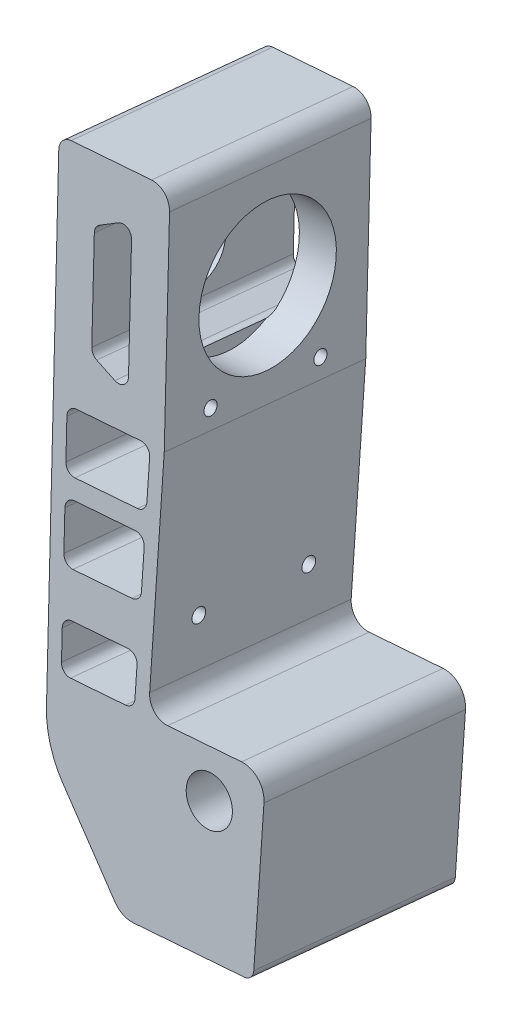
SolidWorks part; units mm, degrees
ref_plane "Front Plane" through (0, 0, 0) normal (0, 0, 1) x (1, 0, 0)
ref_plane "Top Plane" through (0, 0, 0) normal (0, 1, 0) x (1, 0, 0)
ref_plane "Right Plane" through (0, 0, 0) normal (1, 0, 0) x (0, 0, -1)
sketch "Sketch2" plane through (0, 5.1848, 52.754) normal (0, 0.0978, 0.9952) x (1, 0, 0)
  line L0 (-79.3386, 60.0196) -> (-86.1713, 157.1826)
  line L1 (-83.7601, 159.9586) -> (-66.4029, 161.1792)
  line L3 (-53.886, 68.8298) -> (-37.9279, 69.952)
  line L4 (-32.5786, 65.0833) -> (-31.8669, 35.1988)
  line L5 (-33.726, 33.1561) -> (-57.6669, 31.4725)
  line L6 (-61.8472, 33.2455) -> (-74.7061, 48.5637)
  line L9 (-57.6669, 31.4725) -> (-58.0176, 36.4602) construction
  line L11 (-69.4667, 77.7588) -> (-69.797, 86.7578) construction
  line L13 (-62.1322, 157.4697) -> (-59.1859, 115.5731)
  line L14 (-59.1859, 115.5731) -> (-58.1655, 72.7247)
  line L18 (-62.9661, 68.1912) -> (-74.8421, 67.3561)
  line L19 (-76.9775, 69.2109) -> (-77.3984, 75.1961)
  line L21 (-63.8004, 103.219) -> (-77.2973, 102.2699)
  line L23 (-79.4327, 104.1246) -> (-79.9939, 112.1049)
  line L24 (-62.1319, 113.268) -> (-61.9412, 105.2617)
  line L28 (-76.6898, 136.3966) -> (-77.3913, 146.3719)
  line L29 (-63.419, 87.2063) -> (-76.175, 86.3093)
  line L30 (-59.1859, 115.5731) -> (-83.1268, 113.8896) construction
  line L31 (-76.4139, 148.2339) -> (-72.5641, 150.5096)
  line L32 (-78.1391, 114.2403) -> (-64.2716, 115.2155)
  line L33 (-69.5513, 148.9282) -> (-68.7095, 136.9577)
  line L35 (-78.3103, 88.1641) -> (-78.8715, 96.1443)
  line L36 (-76.6898, 136.3966) -> (-68.7095, 136.9577) construction
  line L37 (-76.6898, 136.3966) -> (-68.7095, 136.9577) construction
  line L38 (-67.8677, 124.9873) -> (-68.7095, 136.9577)
  line L39 (-74.76, 124.7143) -> (-70.6295, 122.9998)
  line L40 (-76.6898, 136.3966) -> (-75.9883, 126.4212)
  line L41 (-61.7505, 97.2553) -> (-61.5599, 89.249)
  line L42 (-77.0168, 98.2797) -> (-63.8903, 99.2028)
  line L43 (-61.25, 76.2387) -> (-61.107, 70.2339)
  line L44 (-75.5436, 77.3315) -> (-63.3897, 78.1861)
  arc A0 (-86.1713, 157.1826) -> (-83.7601, 159.9586) centre (-83.5777, 157.365) cw
  arc A1 (-66.4029, 161.1792) -> (-62.1322, 157.4697) centre (-66.1223, 157.1891) cw
  arc A2 (-58.1655, 72.7247) -> (-53.886, 68.8298) centre (-54.1666, 72.8199) ccw
  arc A3 (-37.9279, 69.952) -> (-32.5786, 65.0833) centre (-37.5772, 64.9643) cw
  arc A4 (-31.8669, 35.1988) -> (-33.726, 33.1561) centre (-33.8663, 35.1512) cw
  arc A6 (-74.7061, 48.5637) -> (-79.3386, 60.0196) centre (-59.3878, 61.4226) cw
  circle A7 centre (-43.9609, 60.0043) radius 5
  arc A16 (-77.2973, 102.2699) -> (-79.4327, 104.1246) centre (-77.4376, 104.2649) cw
  arc A17 (-79.9939, 112.1049) -> (-78.1391, 114.2403) centre (-77.9988, 112.2452) cw
  arc A21 (-72.5641, 150.5096) -> (-69.5513, 148.9282) centre (-71.5464, 148.7879) cw
  arc A24 (-77.3913, 146.3719) -> (-76.4139, 148.2339) centre (-75.3962, 146.5122) cw
  arc A26 (-70.6295, 122.9998) -> (-67.8677, 124.9873) centre (-69.8628, 124.847) ccw
  arc A27 (-75.9883, 126.4212) -> (-74.76, 124.7143) centre (-73.9932, 126.5615) ccw
  arc A28 (-64.2716, 115.2155) -> (-62.1319, 113.268) centre (-64.1313, 113.2204) cw
  arc A29 (-61.9412, 105.2617) -> (-63.8004, 103.219) centre (-63.9407, 105.2141) cw
  arc A30 (-76.175, 86.3093) -> (-78.3103, 88.1641) centre (-76.3153, 88.3044) cw
  arc A31 (-78.8715, 96.1443) -> (-77.0168, 98.2797) centre (-76.8765, 96.2846) cw
  arc A32 (-63.8903, 99.2028) -> (-61.7505, 97.2553) centre (-63.75, 97.2077) cw
  arc A33 (-61.5599, 89.249) -> (-63.419, 87.2063) centre (-63.5593, 89.2014) cw
  arc A34 (-74.8421, 67.3561) -> (-76.9775, 69.2109) centre (-74.9824, 69.3512) cw
  arc A35 (-77.3984, 75.1961) -> (-75.5436, 77.3315) centre (-75.4033, 75.3364) cw
  arc A36 (-63.3897, 78.1861) -> (-61.25, 76.2387) centre (-63.2494, 76.1911) cw
  arc A37 (-61.107, 70.2339) -> (-62.9661, 68.1912) centre (-63.1064, 70.1863) cw
  arc A38 (-61.8472, 33.2455) -> (-57.6669, 31.4725) centre (-58.0176, 36.4602) ccw
  point P19 (-71.1564, 114.7313)
  point P62 (-59.1859, 115.5731)
  point P109 (-69.1304, 142.943)
  point P116 (-77.0405, 141.3842)
  point P123 (-72.6997, 136.6771)
  dimension "D3" = 4
  dimension "D6" = 5
  dimension "D9" = 2
  dimension "D10" = 20
  dimension "D12" = 2
  dimension "D11" = 2
  dimension "D23" = 2
  dimension "D24" = 2
  dimension "D25" = 2
  dimension "D26" = 2
  dimension "D29" = 2
  dimension "D30" = 2
  dimension "D31" = 2
  dimension "D32" = 2
  dimension "D38" = 2
  dimension "D39" = 2
  dimension "D40" = 2
  dimension "D41" = 2
  dimension "D44" = 10
  dimension "D8" = 5
  dimension "D18" = 24
  dimension "D19" = 24
  dimension "D13" = 8
  dimension "D14" = 8
  dimension "D15" = 8
  dimension "D16" = 10
  dimension "D17" = 12
  dimension "D20" = 3
  dimension "D22" = 3
  dimension "D27" = 12
  dimension "D28" = 3
  dimension "D33" = 3
  dimension "D34" = 4
  dimension "D35" = 12
  dimension "D36" = 9
  dimension "D21" = 46
  dimension "D37" = 10
  dimension "D42" = 3
  dimension "D43" = 3
  dimension "D5" = 37
  dimension "D7" = 47
  dimension "D45" = 24
  dimension "D46" = 20
  dimension "D47" = 11.5
  dimension "D48" = 9.5
extrude "Boss-Extrude1" add sketch "Sketch2" along normal blind 44
sketch "Sketch3" plane through (-50.8073, -3.5558, 0.3495) normal (0.9975, 0.0698, -0.0069) x (-0.0068, -0.0005, -1)
  line L0 (-80.7931, 170.1353) -> (-37.0031, 165.8421) construction
  line L1 (-84.8912, 128.3357) -> (-80.7931, 170.1353) construction
  line L2 (-82.8422, 149.2355) -> (-39.0521, 144.9423) construction
  line L3 (-41.1011, 124.0425) -> (-37.0031, 165.8421) construction
  line L4 (-58.8981, 167.9887) -> (-62.9962, 126.1891) construction
  line L5 (-84.8912, 128.3357) -> (-41.1011, 124.0425) construction
  line L6 (-74.5486, 131.3409) -> (-79.1164, 84.7498) construction
  line L7 (-89.0687, 85.7255) -> (-84.8912, 128.3357) construction
  line L8 (-89.0687, 85.7255) -> (-45.2787, 81.4323) construction
  circle A0 centre (-60.9471, 147.0889) radius 15
  circle A1 centre (-74.5486, 131.3409) radius 1.4323
  circle A2 centre (-78.1407, 94.7021) radius 1.5
  circle A3 centre (-54.2552, 92.3603) radius 1.5
  circle A4 centre (-50.6631, 128.9991) radius 1.4323
  point P0 (-58.8981, 167.9887)
  point P1 (-82.8422, 149.2355)
  dimension "D1" = 30
  dimension "D4" = 2.8645
  dimension "D5" = 3
  dimension "D2" = 4
  dimension "D3" = 10
  dimension "D6" = 10
sketch "Sketch4" plane through (-74.7482, -5.2313, 0.5141) normal (-0.9975, -0.0698, 0.0069) x (0.0068, 0.0005, 1)
  circle A0 centre (60.9471, 147.0889) radius 7
  dimension "D1" = 14
extrude "Cut-Extrude1" cut sketch "Sketch4" against normal blind 44
extrude "Cut-Extrude2" cut sketch "Sketch3" against normal blind 8.5
equation "\"radius2mm\"=2"
equation "\"distance3mm\"=3"
equation "\"D20@Sketch2\"=\"distance3mm\""
equation "\"D22@Sketch2\"=\"distance3mm\""
equation "\"D28@Sketch2\"=\"distance3mm\""
equation "\"D9@Sketch2\"=\"radius2mm\""
